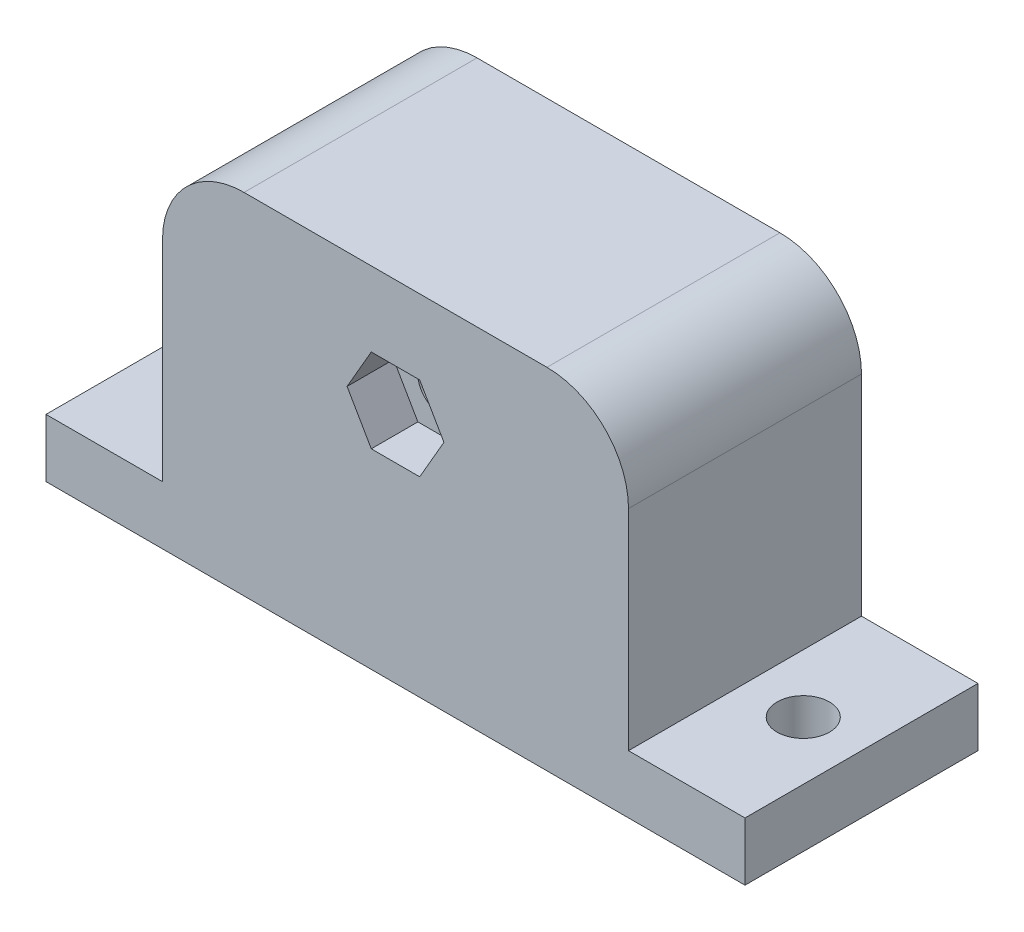
SolidWorks part; units mm, degrees
ref_plane "Front Plane" through (0, 0, 0) normal (0, 0, 1) x (1, 0, 0)
ref_plane "Top Plane" through (0, 0, 0) normal (0, 1, 0) x (1, 0, 0)
ref_plane "Right Plane" through (0, 0, 0) normal (1, 0, 0) x (0, 0, -1)
sketch "Sketch1" plane through (0, 0, 0) normal (0, 1, 0) x (1, 0, 0)
  line L1 (-30, -10) -> (30, -10)
  line L2 (-30, -10) -> (-30, 10)
  line L3 (-30, 10) -> (30, 10)
  line L4 (30, -10) -> (30, 10)
  line L5 (-30, -10) -> (30, 10) construction
  line L6 (-30, 10) -> (30, -10) construction
  circle A0 centre (-25, 0) radius 2.25
  circle A1 centre (25, 0) radius 2.25
  point P0 (0, 0)
  dimension "D3" = 4.5
  dimension "D4" = 4.5
  dimension "D5" = 5
  dimension "D6" = 5
  dimension "D1" = 60
  dimension "D2" = 20
extrude "Boss-Extrude1" add sketch "Sketch1" along normal blind 5
sketch "Sketch2" plane through (0, 5, 0) normal (0, 1, 0) x (1, 0, 0)
  line L0 (30, 10) -> (-30, 10) construction
  line L1 (-20, 10) -> (20, 10)
  line L2 (-20, 10) -> (-20, -10)
  line L3 (-20, -10) -> (20, -10)
  line L4 (20, 10) -> (20, -10)
  line L5 (-30, -10) -> (30, -10) construction
  line L6 (-30, 10) -> (-30, -10) construction
  line L7 (30, -10) -> (30, 10) construction
  dimension "D1" = 10
  dimension "D2" = 10
extrude "Boss-Extrude2" add sketch "Sketch2" along normal blind 25
sketch "Sketch3" plane through (0, 0, -10) normal (0, 0, -1) x (-1, 0, 0)
  line L0 (-20, 30) -> (20, 30) construction
  line L1 (-30, 0) -> (30, 0) construction
  circle A0 centre (0, 20) radius 2.1
  dimension "D1" = 4.2
  dimension "D2" = 10
  dimension "D3" = 20
extrude "Cut-Extrude1" cut sketch "Sketch3" against normal through all and the other way through all
sketch "Sketch4" plane through (0, 0, -10) normal (0, 0, -1) x (-1, 0, 0)
  circle A0 centre (0, 20) radius 3.75
  dimension "D1" = 7.5
extrude "Cut-Extrude2" cut sketch "Sketch4" against normal blind 5
sketch "Sketch5" plane through (0, 0, 10) normal (0, 0, 1) x (1, 0, 0)
  line L0 (-20, 30) -> (20, 30) construction
  line L1 (2.0785, 23.6) -> (-2.0785, 23.6)
  line L2 (-2.0785, 23.6) -> (-4.1569, 20)
  line L3 (-4.1569, 20) -> (-2.0785, 16.4)
  line L4 (-2.0785, 16.4) -> (2.0785, 16.4)
  line L5 (2.0785, 16.4) -> (4.1569, 20)
  line L6 (4.1569, 20) -> (2.0785, 23.6)
  circle A0 centre (0, 20) radius 3.6 construction
  dimension "D1" = 7.2
extrude "Cut-Extrude3" cut sketch "Sketch5" against normal blind 4
fillet "Fillet1" radius 7 2 edges at (-20, 30, 0) (20, 30, 0)
